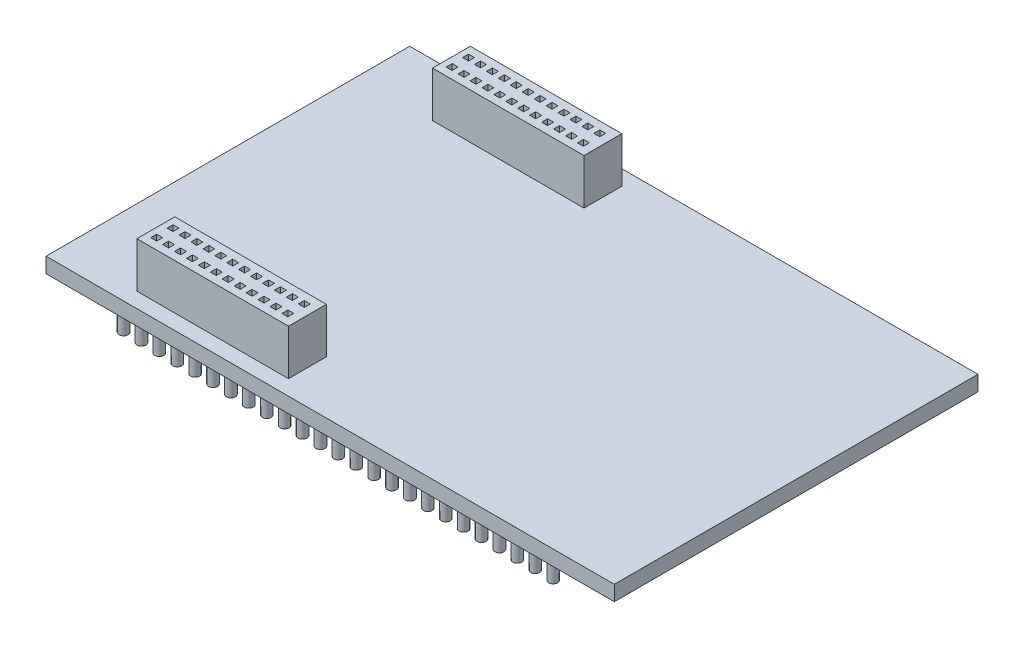
SolidWorks part; units mm, degrees
ref_plane "Front Plane" through (0, 0, 0) normal (0, 0, 1) x (1, 0, 0)
ref_plane "Top Plane" through (0, 0, 0) normal (0, 1, 0) x (1, 0, 0)
ref_plane "Right Plane" through (0, 0, 0) normal (1, 0, 0) x (0, 0, -1)
sketch "Sketch1" plane through (0, 0, 0) normal (0, 1, 0) x (1, 0, 0)
  line L1 (0, 0) -> (95.25, 0)
  line L2 (0, 0) -> (0, 60.96)
  line L3 (0, 60.96) -> (95.25, 60.96)
  line L4 (95.25, 0) -> (95.25, 60.96)
  dimension "D1" = 95.25
  dimension "D2" = 60.96
extrude "Boss-Extrude1" add sketch "Sketch1" along normal blind 2.54
sketch "Sketch2" plane through (0, 2.54, 0) normal (0, 1, 0) x (1, 0, 0)
  line L0 (0, 30.48) -> (95.25, 30.48) construction
  line L1 (12.7, 58.42) -> (38.1, 58.42)
  line L2 (12.7, 58.42) -> (12.7, 52.07)
  line L3 (12.7, 52.07) -> (38.1, 52.07)
  line L4 (38.1, 58.42) -> (38.1, 52.07)
  line L5 (12.7, 8.89) -> (38.1, 8.89)
  line L6 (12.7, 8.89) -> (12.7, 2.54)
  line L7 (12.7, 2.54) -> (38.1, 2.54)
  line L8 (38.1, 8.89) -> (38.1, 2.54)
  line L9 (0, 60.96) -> (0, 0) construction
  line L10 (95.25, 0) -> (95.25, 60.96) construction
  line L11 (95.25, 60.96) -> (0, 60.96) construction
  dimension "D1" = 6.35
  dimension "D2" = 6.35
  dimension "D3" = 25.4
  dimension "D4" = 25.4
  dimension "D5" = 2.54
  dimension "D6" = 12.7
extrude "Boss-Extrude2" add sketch "Sketch2" along normal blind 7.62
sketch "Sketch3" plane through (0, 10.16, 0) normal (0, 1, 0) x (1, 0, 0)
  line L1 (13.7, 57.12) -> (14.7, 57.12)
  line L2 (13.7, 57.12) -> (13.7, 56.12)
  line L3 (13.7, 56.12) -> (14.7, 56.12)
  line L4 (14.7, 57.12) -> (14.7, 56.12)
  line L5 (38.1, 58.42) -> (12.7, 58.42) construction
  line L6 (12.7, 58.42) -> (12.7, 52.07) construction
  line L7 (12.7, 55.245) -> (38.1, 55.245) construction
  line L8 (12.7, 58.42) -> (12.7, 52.07) construction
  line L9 (38.1, 52.07) -> (38.1, 58.42) construction
  line L10 (15.7, 57.12) -> (15.7, 56.12)
  line L11 (15.7, 57.12) -> (16.7, 57.12)
  line L12 (16.7, 57.12) -> (16.7, 56.12)
  line L13 (15.7, 56.12) -> (16.7, 56.12)
  line L14 (17.7, 57.12) -> (17.7, 56.12)
  line L15 (17.7, 57.12) -> (18.7, 57.12)
  line L16 (18.7, 57.12) -> (18.7, 56.12)
  line L17 (17.7, 56.12) -> (18.7, 56.12)
  line L18 (19.7, 57.12) -> (19.7, 56.12)
  line L19 (19.7, 57.12) -> (20.7, 57.12)
  line L20 (20.7, 57.12) -> (20.7, 56.12)
  line L21 (19.7, 56.12) -> (20.7, 56.12)
  line L22 (21.7, 57.12) -> (21.7, 56.12)
  line L23 (21.7, 57.12) -> (22.7, 57.12)
  line L24 (22.7, 57.12) -> (22.7, 56.12)
  line L25 (21.7, 56.12) -> (22.7, 56.12)
  line L26 (23.7, 57.12) -> (23.7, 56.12)
  line L27 (23.7, 57.12) -> (24.7, 57.12)
  line L28 (24.7, 57.12) -> (24.7, 56.12)
  line L29 (23.7, 56.12) -> (24.7, 56.12)
  line L30 (25.7, 57.12) -> (25.7, 56.12)
  line L31 (25.7, 57.12) -> (26.7, 57.12)
  line L32 (26.7, 57.12) -> (26.7, 56.12)
  line L33 (25.7, 56.12) -> (26.7, 56.12)
  line L34 (27.7, 57.12) -> (27.7, 56.12)
  line L35 (27.7, 57.12) -> (28.7, 57.12)
  line L36 (28.7, 57.12) -> (28.7, 56.12)
  line L37 (27.7, 56.12) -> (28.7, 56.12)
  line L38 (29.7, 57.12) -> (29.7, 56.12)
  line L39 (29.7, 57.12) -> (30.7, 57.12)
  line L40 (30.7, 57.12) -> (30.7, 56.12)
  line L41 (29.7, 56.12) -> (30.7, 56.12)
  line L42 (31.7, 57.12) -> (31.7, 56.12)
  line L43 (31.7, 57.12) -> (32.7, 57.12)
  line L44 (32.7, 57.12) -> (32.7, 56.12)
  line L45 (31.7, 56.12) -> (32.7, 56.12)
  line L46 (33.7, 57.12) -> (33.7, 56.12)
  line L47 (33.7, 57.12) -> (34.7, 57.12)
  line L48 (34.7, 57.12) -> (34.7, 56.12)
  line L49 (33.7, 56.12) -> (34.7, 56.12)
  line L50 (35.7, 57.12) -> (35.7, 56.12)
  line L51 (35.7, 57.12) -> (36.7, 57.12)
  line L52 (36.7, 57.12) -> (36.7, 56.12)
  line L53 (35.7, 56.12) -> (36.7, 56.12)
  line L54 (35.7, 54.37) -> (36.7, 54.37)
  line L55 (36.7, 53.37) -> (36.7, 54.37)
  line L56 (35.7, 53.37) -> (36.7, 53.37)
  line L57 (35.7, 53.37) -> (35.7, 54.37)
  line L58 (33.7, 54.37) -> (34.7, 54.37)
  line L59 (34.7, 53.37) -> (34.7, 54.37)
  line L60 (33.7, 53.37) -> (34.7, 53.37)
  line L61 (33.7, 53.37) -> (33.7, 54.37)
  line L62 (31.7, 54.37) -> (32.7, 54.37)
  line L63 (32.7, 53.37) -> (32.7, 54.37)
  line L64 (31.7, 53.37) -> (32.7, 53.37)
  line L65 (31.7, 53.37) -> (31.7, 54.37)
  line L66 (29.7, 54.37) -> (30.7, 54.37)
  line L67 (30.7, 53.37) -> (30.7, 54.37)
  line L68 (29.7, 53.37) -> (30.7, 53.37)
  line L69 (29.7, 53.37) -> (29.7, 54.37)
  line L70 (27.7, 54.37) -> (28.7, 54.37)
  line L71 (28.7, 53.37) -> (28.7, 54.37)
  line L72 (27.7, 53.37) -> (28.7, 53.37)
  line L73 (27.7, 53.37) -> (27.7, 54.37)
  line L74 (25.7, 54.37) -> (26.7, 54.37)
  line L75 (26.7, 53.37) -> (26.7, 54.37)
  line L76 (25.7, 53.37) -> (26.7, 53.37)
  line L77 (25.7, 53.37) -> (25.7, 54.37)
  line L78 (23.7, 54.37) -> (24.7, 54.37)
  line L79 (24.7, 53.37) -> (24.7, 54.37)
  line L80 (23.7, 53.37) -> (24.7, 53.37)
  line L81 (23.7, 53.37) -> (23.7, 54.37)
  line L82 (21.7, 54.37) -> (22.7, 54.37)
  line L83 (22.7, 53.37) -> (22.7, 54.37)
  line L84 (21.7, 53.37) -> (22.7, 53.37)
  line L85 (21.7, 53.37) -> (21.7, 54.37)
  line L86 (19.7, 54.37) -> (20.7, 54.37)
  line L87 (20.7, 53.37) -> (20.7, 54.37)
  line L88 (19.7, 53.37) -> (20.7, 53.37)
  line L89 (19.7, 53.37) -> (19.7, 54.37)
  line L90 (17.7, 54.37) -> (18.7, 54.37)
  line L91 (18.7, 53.37) -> (18.7, 54.37)
  line L92 (17.7, 53.37) -> (18.7, 53.37)
  line L93 (17.7, 53.37) -> (17.7, 54.37)
  line L94 (15.7, 54.37) -> (16.7, 54.37)
  line L95 (16.7, 53.37) -> (16.7, 54.37)
  line L96 (15.7, 53.37) -> (16.7, 53.37)
  line L97 (15.7, 53.37) -> (15.7, 54.37)
  line L98 (14.7, 53.37) -> (14.7, 54.37)
  line L99 (13.7, 54.37) -> (14.7, 54.37)
  line L100 (13.7, 53.37) -> (13.7, 54.37)
  line L101 (13.7, 53.37) -> (14.7, 53.37)
  dimension "D1" = 1
  dimension "D2" = 1
  dimension "D3" = 1.3
  dimension "D4" = 1
  dimension "D5" = 12
extrude "Cut-Extrude1" cut sketch "Sketch3" against normal blind 4.62
ref_plane "Plane1" through (0, 0, -30.48) normal (0, 0, 1) x (1, 0, 0)
mirror "Mirror1" about plane through (0, 0, -30.48) normal (0, 0, 1) of "Cut-Extrude1"
sketch "Sketch4" plane through (0, 0, 0) normal (0, -1, 0) x (1, 0, 0)
  line L0 (0, -60.96) -> (0, 0) construction
  line L1 (0, 0) -> (95.25, 0) construction
  line L2 (0, -30.48) -> (95.25, -30.48) construction
  line L3 (95.25, 0) -> (95.25, -60.96) construction
  circle A0 centre (10, -3) radius 0.75
  circle A1 centre (13, -3) radius 0.75
  circle A2 centre (16, -3) radius 0.75
  circle A3 centre (19, -3) radius 0.75
  circle A4 centre (22, -3) radius 0.75
  circle A5 centre (25, -3) radius 0.75
  circle A6 centre (28, -3) radius 0.75
  circle A7 centre (31, -3) radius 0.75
  circle A8 centre (34, -3) radius 0.75
  circle A9 centre (37, -3) radius 0.75
  circle A10 centre (40, -3) radius 0.75
  circle A11 centre (43, -3) radius 0.75
  circle A12 centre (46, -3) radius 0.75
  circle A13 centre (49, -3) radius 0.75
  circle A14 centre (52, -3) radius 0.75
  circle A15 centre (55, -3) radius 0.75
  circle A16 centre (58, -3) radius 0.75
  circle A17 centre (61, -3) radius 0.75
  circle A18 centre (64, -3) radius 0.75
  circle A19 centre (67, -3) radius 0.75
  circle A20 centre (70, -3) radius 0.75
  circle A21 centre (73, -3) radius 0.75
  circle A22 centre (76, -3) radius 0.75
  circle A23 centre (79, -3) radius 0.75
  circle A24 centre (82, -3) radius 0.75
  circle A25 centre (13, -8) radius 0.75
  circle A26 centre (16, -8) radius 0.75
  circle A27 centre (19, -8) radius 0.75
  circle A28 centre (22, -8) radius 0.75
  circle A29 centre (25, -8) radius 0.75
  circle A30 centre (28, -8) radius 0.75
  circle A31 centre (31, -8) radius 0.75
  circle A32 centre (34, -8) radius 0.75
  circle A33 centre (37, -8) radius 0.75
  circle A34 centre (40, -8) radius 0.75
  circle A35 centre (43, -8) radius 0.75
  circle A36 centre (46, -8) radius 0.75
  circle A37 centre (49, -8) radius 0.75
  circle A38 centre (52, -8) radius 0.75
  circle A39 centre (55, -8) radius 0.75
  circle A40 centre (58, -8) radius 0.75
  circle A41 centre (61, -8) radius 0.75
  circle A42 centre (64, -8) radius 0.75
  circle A43 centre (67, -8) radius 0.75
  circle A44 centre (70, -8) radius 0.75
  circle A45 centre (73, -8) radius 0.75
  circle A46 centre (76, -8) radius 0.75
  circle A47 centre (79, -8) radius 0.75
  circle A48 centre (82, -8) radius 0.75
  circle A49 centre (10, -8) radius 0.75
  circle A50 centre (10, -52.96) radius 0.75
  circle A51 centre (82, -52.96) radius 0.75
  circle A52 centre (79, -52.96) radius 0.75
  circle A53 centre (76, -52.96) radius 0.75
  circle A54 centre (73, -52.96) radius 0.75
  circle A55 centre (70, -52.96) radius 0.75
  circle A56 centre (67, -52.96) radius 0.75
  circle A57 centre (64, -52.96) radius 0.75
  circle A58 centre (61, -52.96) radius 0.75
  circle A59 centre (58, -52.96) radius 0.75
  circle A60 centre (55, -52.96) radius 0.75
  circle A61 centre (52, -52.96) radius 0.75
  circle A62 centre (49, -52.96) radius 0.75
  circle A63 centre (46, -52.96) radius 0.75
  circle A64 centre (43, -52.96) radius 0.75
  circle A65 centre (40, -52.96) radius 0.75
  circle A66 centre (37, -52.96) radius 0.75
  circle A67 centre (34, -52.96) radius 0.75
  circle A68 centre (31, -52.96) radius 0.75
  circle A69 centre (28, -52.96) radius 0.75
  circle A70 centre (25, -52.96) radius 0.75
  circle A71 centre (22, -52.96) radius 0.75
  circle A72 centre (19, -52.96) radius 0.75
  circle A73 centre (16, -52.96) radius 0.75
  circle A74 centre (13, -52.96) radius 0.75
  circle A75 centre (82, -57.96) radius 0.75
  circle A76 centre (79, -57.96) radius 0.75
  circle A77 centre (76, -57.96) radius 0.75
  circle A78 centre (73, -57.96) radius 0.75
  circle A79 centre (70, -57.96) radius 0.75
  circle A80 centre (67, -57.96) radius 0.75
  circle A81 centre (64, -57.96) radius 0.75
  circle A82 centre (61, -57.96) radius 0.75
  circle A83 centre (58, -57.96) radius 0.75
  circle A84 centre (55, -57.96) radius 0.75
  circle A85 centre (52, -57.96) radius 0.75
  circle A86 centre (49, -57.96) radius 0.75
  circle A87 centre (46, -57.96) radius 0.75
  circle A88 centre (43, -57.96) radius 0.75
  circle A89 centre (40, -57.96) radius 0.75
  circle A90 centre (37, -57.96) radius 0.75
  circle A91 centre (34, -57.96) radius 0.75
  circle A92 centre (31, -57.96) radius 0.75
  circle A93 centre (28, -57.96) radius 0.75
  circle A94 centre (25, -57.96) radius 0.75
  circle A95 centre (22, -57.96) radius 0.75
  circle A96 centre (19, -57.96) radius 0.75
  circle A97 centre (16, -57.96) radius 0.75
  circle A98 centre (13, -57.96) radius 0.75
  circle A99 centre (10, -57.96) radius 0.75
  dimension "D1" = 1.5
  dimension "D2" = 10
  dimension "D3" = 3
  dimension "D4" = 25
  dimension "D5" = 2
extrude "Boss-Extrude3" add sketch "Sketch4" along normal blind 5
